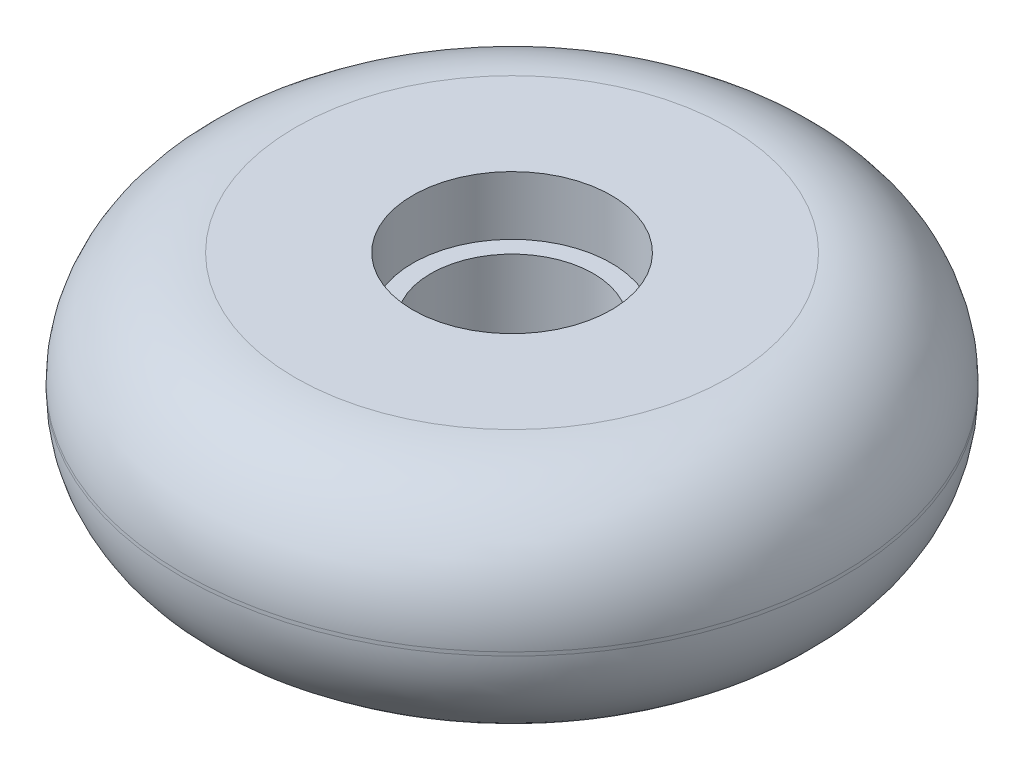
SolidWorks part; units mm, degrees
material "Rubber"
ref_plane "Front Plane" through (0, 0, 0) normal (0, 0, 1) x (1, 0, 0)
ref_plane "Top Plane" through (0, 0, 0) normal (0, 1, 0) x (1, 0, 0)
ref_plane "Right Plane" through (0, 0, 0) normal (1, 0, 0) x (0, 0, -1)
sketch "Sketch1" plane through (0, 0, 0) normal (0, 1, 0) x (1, 0, 0)
  circle A0 centre (0, 0) radius 36.5125
  dimension "D1" = 73.025
extrude "Boss-Extrude1" add sketch "Sketch1" along normal blind 25.4
fillet "Fillet1" radius 12.5 2 edges at (0, 0, 36.5125) (0, 25.4, 36.5125)
sketch "Sketch2" plane through (0, 25.4, 0) normal (0, 1, 0) x (1, 0, 0)
  circle A0 centre (0, 0) radius 11
  dimension "D1" = 22
extrude "Cut-Extrude1" cut sketch "Sketch2" against normal blind 6.5
sketch "Sketch3" plane through (0, 0, 0) normal (0, -1, 0) x (1, 0, 0)
  circle A0 centre (0, 0) radius 11
  dimension "D1" = 22
extrude "Cut-Extrude2" cut sketch "Sketch3" against normal blind 6.5
sketch "Sketch4" plane through (0, 6.5, 0) normal (0, -1, 0) x (1, 0, 0)
  circle A0 centre (0, 0) radius 9
  dimension "D1" = 18
extrude "Cut-Extrude3" cut sketch "Sketch4" against normal through all
